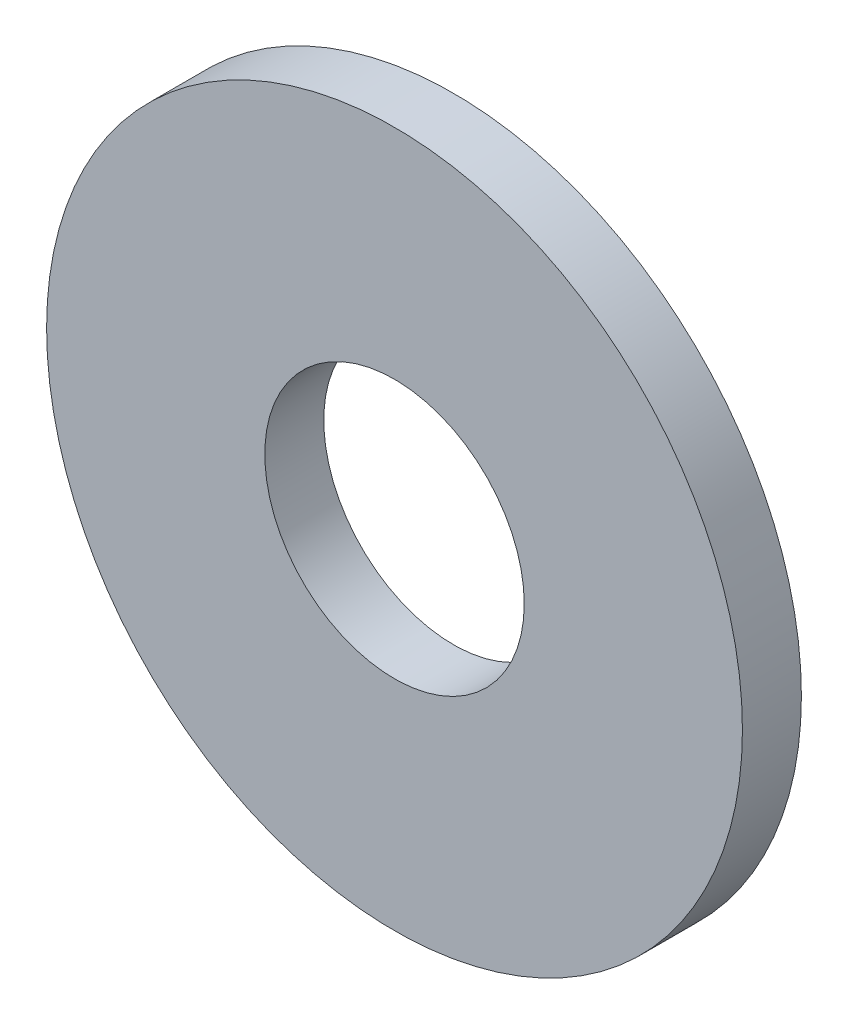
SolidWorks part; units mm, degrees
ref_plane "Front Plane" through (0, 0, 0) normal (0, 0, 1) x (1, 0, 0)
ref_plane "Top Plane" through (0, 0, 0) normal (0, 1, 0) x (1, 0, 0)
ref_plane "Right Plane" through (0, 0, 0) normal (1, 0, 0) x (0, 0, -1)
sketch "Sketch1" plane through (0, 0, 0) normal (0, 0, 1) x (1, 0, 0)
  circle A0 centre (0, 0) radius 5.9 construction
  circle A1 centre (0, 0) radius 2.2 construction
  point P5 (-2.2, 0)
  point P6 (2.2, 0)
  point P7 (5.9, 0)
  point P8 (-5.9, 0)
  point P9 (0, -2.2)
  dimension "OD" = 11.8
  dimension "ID" = 4.4
sketch "Sketch2" plane through (0, 0, 0) normal (1, 0, 0) x (0, 0, -1)
  line L0 (0.5, 0) -> (-0.5, 0) construction
  line L1 (0, 5.9) -> (0, -5.9) construction
  line L2 (0, 5.9) -> (0, -5.9) construction
  line L3 (0.5, 5.9) -> (-0.5, 5.9) construction
  line L4 (0.5, -5.9) -> (-0.5, -5.9) construction
  line L5 (-0.5, -5.9) -> (-0.5, 5.9) construction
  line L6 (0.5, -5.9) -> (0.5, 5.9) construction
  point P4 (0, 0)
  point P10 (0, 5.9)
  point P11 (-0.5, 5.9)
  point P14 (0, -5.9)
  point P15 (-0.5, -5.9)
  point P16 (0.5, -5.9)
  point P17 (0.5, 5.9)
  point P18 (0.5, 0)
  point P19 (-0.5, 0)
  dimension "Thickness Range" = 1
sketch "Sketch3" plane through (0, 0, 0) normal (0, 0, 1) x (1, 0, 0)
  circle A0 centre (0, 0) radius 5.9 construction
  circle A1 centre (0, 0) radius 2.2 construction
  circle A2 centre (0, 0) radius 5.9
  circle A3 centre (0, 0) radius 2.2
extrude "Boss-Extrude1" add sketch "Sketch3" along normal mid plane 1
equation "\"D1@Boss-Extrude1\"= \"Thickness Range@Sketch2\""
